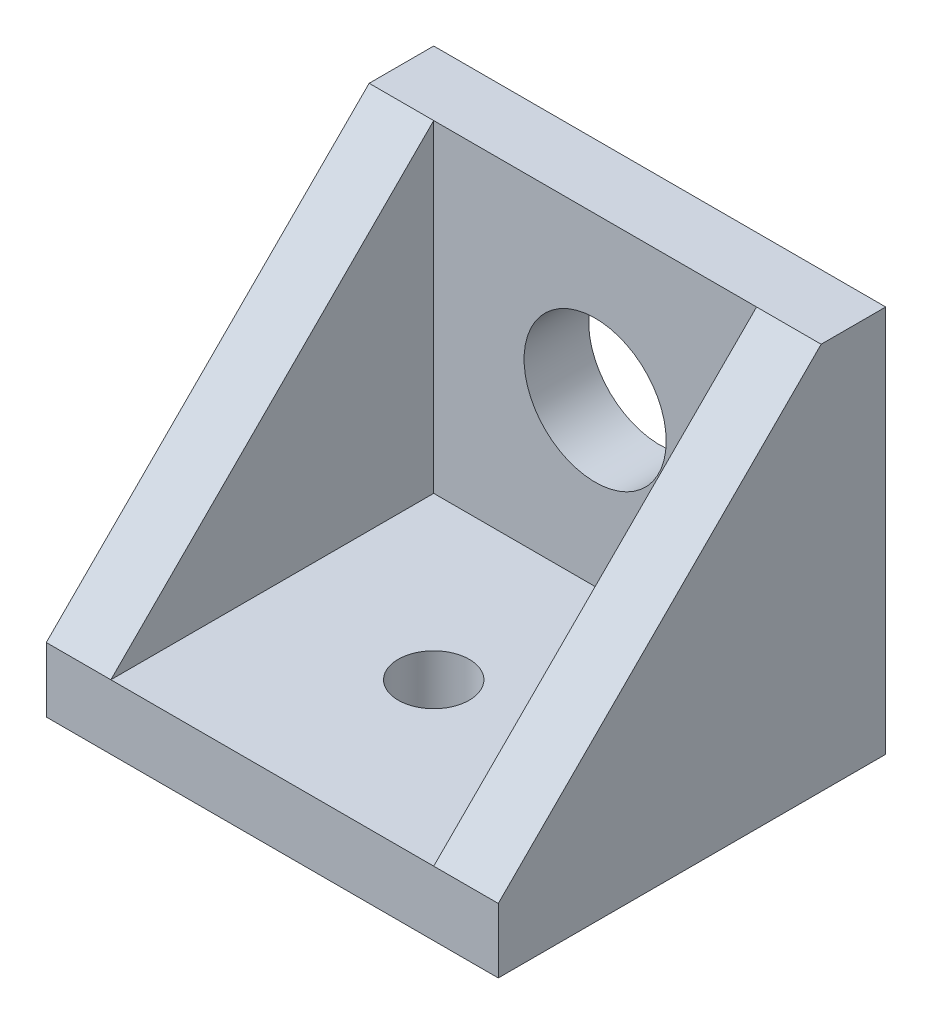
SolidWorks part; units mm, degrees
ref_plane "Front Plane" through (0, 0, 0) normal (0, 0, 1) x (1, 0, 0)
ref_plane "Top Plane" through (0, 0, 0) normal (0, 1, 0) x (1, 0, 0)
ref_plane "Right Plane" through (0, 0, 0) normal (1, 0, 0) x (0, 0, -1)
sketch "Sketch1" plane through (0, 0, 0) normal (0, 0, 1) x (1, 0, 0)
  line L1 (-7.5, -7.5) -> (7.5, -7.5)
  line L2 (-7.5, -7.5) -> (-7.5, 7.5)
  line L3 (-7.5, 7.5) -> (7.5, 7.5)
  line L4 (7.5, -7.5) -> (7.5, 7.5)
  line L5 (-7.5, -7.5) -> (7.5, 7.5) construction
  line L6 (-7.5, 7.5) -> (7.5, -7.5) construction
  circle A0 centre (0, 0) radius 3.302
  dimension "D1" = 6.604
  dimension "D2" = 15
extrude "Boss-Extrude1" add sketch "Sketch1" along normal blind 3
sketch "Sketch2" plane through (0, -7.5, 0) normal (0, -1, 0) x (1, 0, 0)
  line L5 (-7.5, 0) -> (7.5, 0)
  line L6 (-7.5, 0) -> (-7.5, 18)
  line L7 (-7.5, 18) -> (7.5, 18)
  line L8 (7.5, 0) -> (7.5, 18)
  circle A0 centre (0, 10.5) radius 1.65
  dimension "D3" = 3.3
  dimension "D1" = 18
  dimension "D2" = 15
  dimension "D4" = 10.5
extrude "Boss-Extrude2" add sketch "Sketch2" along normal blind 3
sketch "Sketch3" plane through (7.5, 0, 0) normal (1, 0, 0) x (0, 0, -1)
  line L1 (-18, -10.5) -> (-18, -7.5) construction
  line L2 (-18, -10.5) -> (-18, -7.5)
  line L3 (-3, 7.5) -> (0, 7.5) construction
  line L4 (0, -10.5) -> (0, 7.5) construction
  line L5 (0, -10.5) -> (-18, -10.5) construction
  line L6 (-3, 7.5) -> (0, 7.5)
  line L7 (0, -10.5) -> (0, 7.5)
  line L8 (0, -10.5) -> (-18, -10.5)
  line L9 (-18, -7.5) -> (-3, 7.5)
ref_plane "Plane1" through (0, 0, 0) normal (1, 0, 0) x (0, 0, -1)
extrude "Boss-Extrude3" add sketch "Sketch3" along normal blind 3
mirror "Mirror1" about plane through (0, 0, 0) normal (1, 0, 0) of "Boss-Extrude3"
